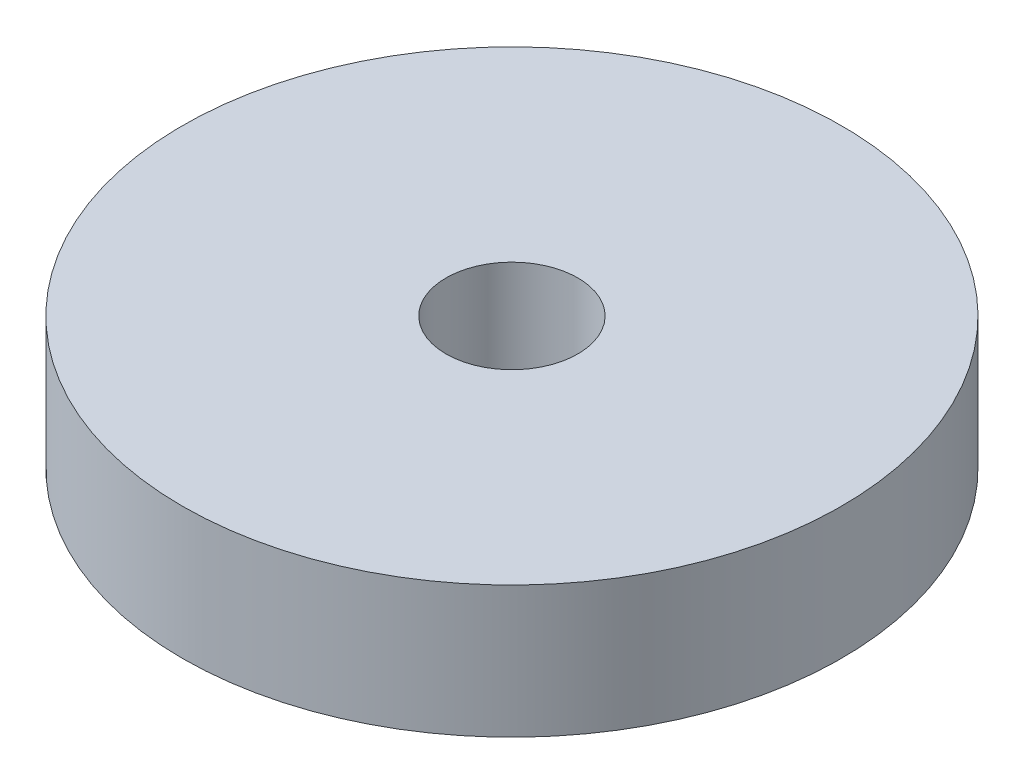
SolidWorks part; units mm, degrees
ref_plane "Front Plane" through (0, 0, 0) normal (0, 0, 1) x (1, 0, 0)
ref_plane "Top Plane" through (0, 0, 0) normal (0, 1, 0) x (1, 0, 0)
ref_plane "Right Plane" through (0, 0, 0) normal (1, 0, 0) x (0, 0, -1)
sketch "Sketch1" plane through (0, 0, 0) normal (0, 1, 0) x (1, 0, 0)
  circle A0 centre (0, 0) radius 1.5
  circle A1 centre (0, 0) radius 7.5
  dimension "D1" = 3
  dimension "D2" = 15
extrude "Boss-Extrude1" add sketch "Sketch1" along normal blind 3
